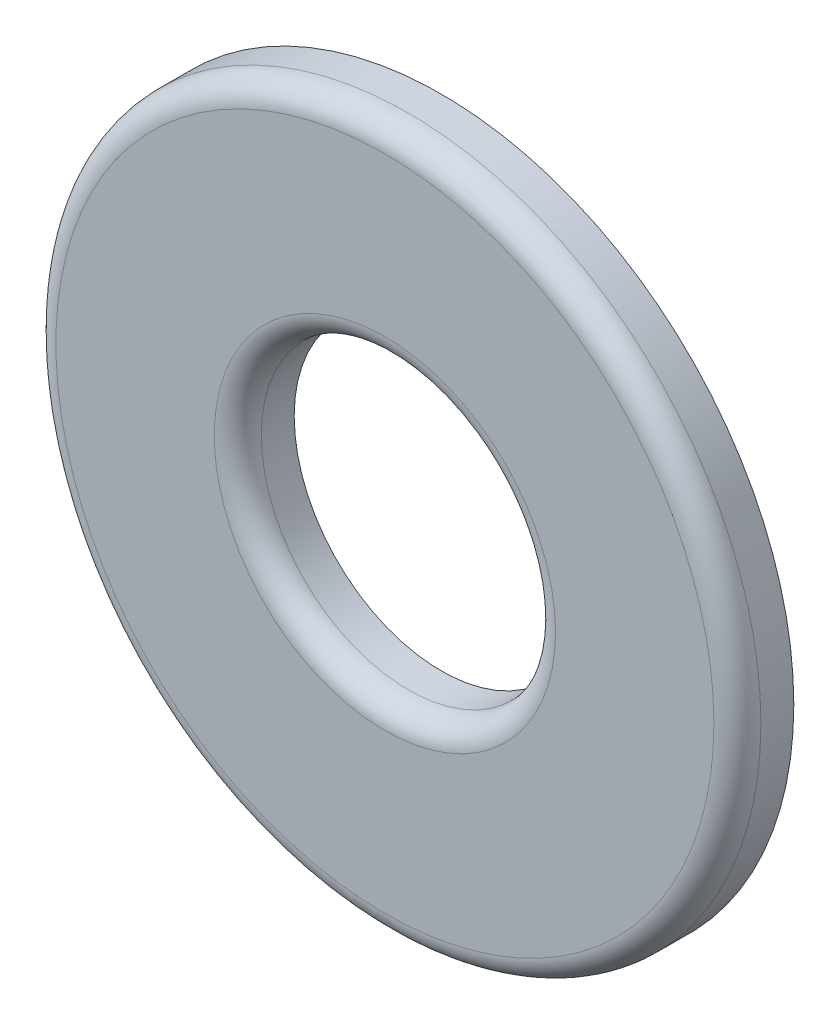
SolidWorks part; units mm, degrees
ref_plane "Front Plane" through (0, 0, 0) normal (0, 0, 1) x (1, 0, 0)
ref_plane "Top Plane" through (0, 0, 0) normal (0, 1, 0) x (1, 0, 0)
ref_plane "Right Plane" through (0, 0, 0) normal (1, 0, 0) x (0, 0, -1)
sketch "Sketch1" plane through (0, 0, 0) normal (0, 0, 1) x (1, 0, 0)
  circle A0 centre (0, 0) radius 9.525
  circle A1 centre (0, 0) radius 3.9751
  dimension "D1" = 19.05
  dimension "D2" = 7.9502
extrude "Boss-Extrude1" add sketch "Sketch1" along normal blind 1.524
fillet "Fillet1" radius 0.635 2 edges at (3.9751, 0, 1.524) (9.525, 0, 1.524)
